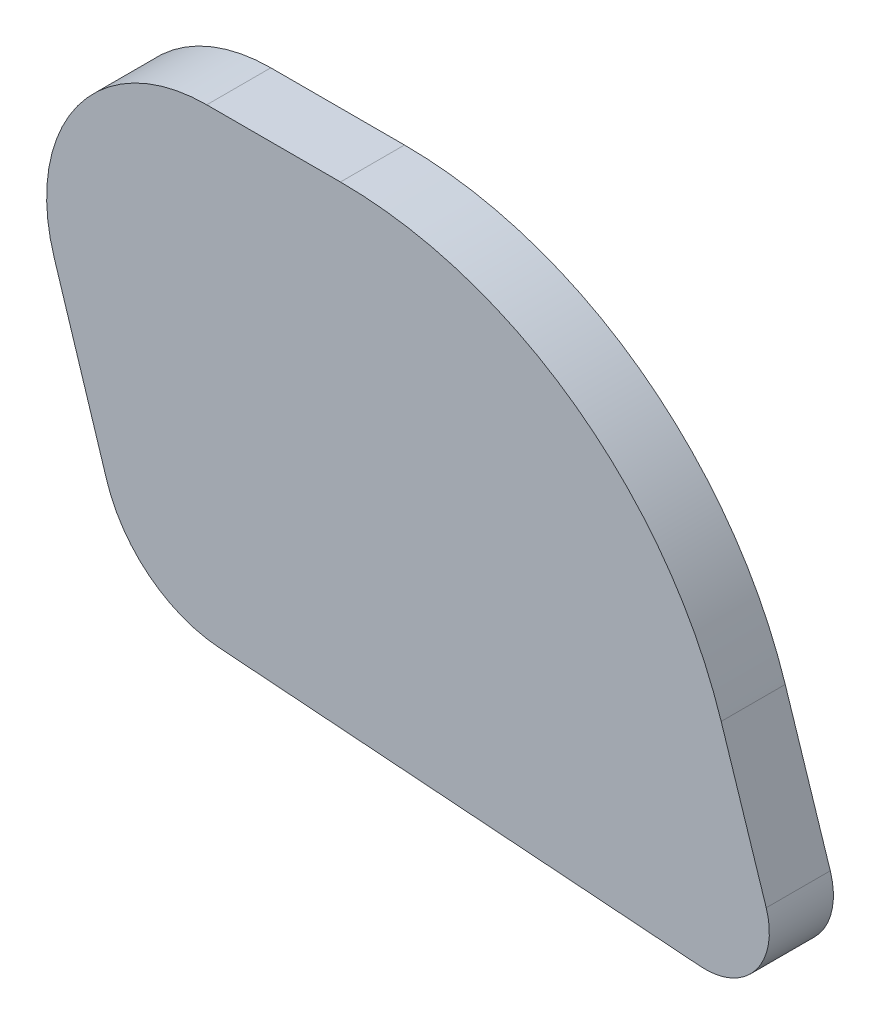
SolidWorks part; units mm, degrees
ref_plane "Front Plane" through (0, 0, 0) normal (0, 0, 1) x (1, 0, 0)
ref_plane "Top Plane" through (0, 0, 0) normal (0, 1, 0) x (1, 0, 0)
ref_plane "Right Plane" through (0, 0, 0) normal (1, 0, 0) x (0, 0, -1)
sketch "Sketch1" plane through (0, 0, 0) normal (0, 0, 1) x (1, 0, 0)
  line L0 (96, 288) -> (480, 288) construction
  line L1 (150.3794, 210.9397) -> (158.7289, 210.9397)
  line L2 (182.5095, 193.6523) -> (185.3226, 184.9786)
  line L3 (181.2249, 179.7553) -> (151.1683, 181.9613)
  line L4 (144.1249, 187.532) -> (140.8431, 197.9299)
  arc A0 (150.3794, 210.9397) -> (140.8431, 197.9299) centre (150.3794, 200.9397) ccw
  arc A1 (158.7289, 210.9397) -> (182.5095, 193.6523) centre (158.7289, 185.9397) cw
  arc A2 (185.3226, 184.9786) -> (181.2249, 179.7553) centre (181.5177, 183.7446) cw
  arc A3 (151.1683, 181.9613) -> (144.1249, 187.532) centre (151.7539, 189.9399) cw
  dimension "D1" = 10
  dimension "D2" = 25
  dimension "D3" = 4
  dimension "D4" = 8
extrude "Boss-Extrude1" add sketch "Sketch1" along normal blind 4
scale "Scale1" scale about centroid uniform scaling yes scale factor 0.709677
